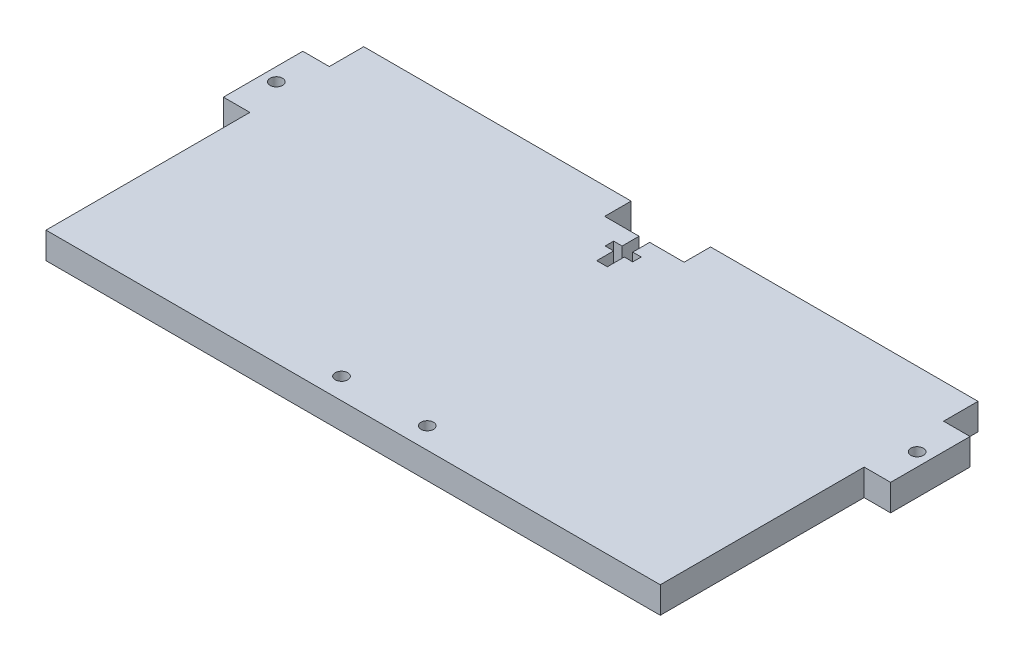
SolidWorks part; units mm, degrees
ref_plane "Front" through (0, 0, 0) normal (0, 0, 1) x (1, 0, 0)
ref_plane "Top" through (0, 0, 0) normal (0, 1, 0) x (1, 0, 0)
ref_plane "Right" through (0, 0, 0) normal (1, 0, 0) x (0, 0, -1)
sketch "Sketch1" plane through (0, 0, 0) normal (0, 1, 0) x (1, 0, 0)
  line L1 (-73.66, -34.925) -> (73.66, -34.925)
  line L2 (-73.66, -34.925) -> (-73.66, 13.97)
  line L3 (-9.525, 34.925) -> (9.525, 34.925)
  line L4 (73.66, -34.925) -> (73.66, 13.97)
  line L5 (-73.66, -34.925) -> (73.66, 34.925) construction
  line L6 (-73.66, 34.925) -> (73.66, -34.925) construction
  line L7 (0, 34.925) -> (0, -34.925) construction
  line L9 (-80.01, 13.97) -> (-73.66, 13.97)
  line L10 (-80.01, 13.97) -> (-80.01, 33.02)
  line L11 (-80.01, 33.02) -> (-73.66, 33.02)
  line L12 (-9.525, 34.925) -> (-9.525, 41.275)
  line L13 (-80.01, 13.97) -> (-73.66, 33.02) construction
  line L14 (-80.01, 33.02) -> (-73.66, 13.97) construction
  line L15 (80.01, 13.97) -> (73.66, 13.97)
  line L16 (80.01, 13.97) -> (80.01, 33.02)
  line L17 (80.01, 33.02) -> (73.66, 33.02)
  line L18 (-73.66, 33.02) -> (-73.66, 34.925)
  line L19 (73.66, 33.02) -> (73.66, 34.925)
  line L20 (-9.525, 41.275) -> (-73.66, 41.275)
  line L21 (-73.66, 34.925) -> (-73.66, 41.275)
  line L22 (9.525, 41.275) -> (73.66, 41.275)
  line L23 (-9.525, 34.925) -> (9.525, 41.275) construction
  line L24 (-9.525, 41.275) -> (9.525, 34.925) construction
  line L25 (9.525, 41.275) -> (9.525, 34.925)
  line L27 (73.66, 41.275) -> (73.66, 34.925)
  circle A0 centre (-76.835, 23.495) radius 1.5
  circle A1 centre (76.835, 23.495) radius 1.5
  point P0 (0, 0)
  point P10 (-76.835, 23.495)
  point P23 (0, 38.1)
  dimension "D5" = 3
  dimension "D8" = 8.255
  dimension "D1" = 147.32
  dimension "D2" = 69.85
  dimension "D3" = 6.35
  dimension "D4" = 19.05
  dimension "D6" = 6.35
  dimension "D7" = 19.05
extrude "Boss-Extrude1" add sketch "Sketch1" along normal blind 6.35
sketch "Sketch2" plane through (0, 6.35, 0) normal (0, 1, 0) x (1, 0, 0)
  line L1 (-11.938, -24.765) -> (-3.81, -24.765) construction
  line L2 (-11.938, -24.765) -> (-11.938, -34.925) construction
  line L3 (-11.938, -34.925) -> (-3.81, -34.925) construction
  line L4 (-3.81, -24.765) -> (-3.81, -34.925) construction
  line L5 (-73.66, -34.925) -> (73.66, -34.925) construction
  line L6 (-73.66, 13.97) -> (-73.66, -34.925) construction
  line L7 (-11.938, -29.845) -> (-7.874, -29.845) construction
  line L8 (-7.874, -29.845) -> (-3.81, -29.845) construction
  circle A0 centre (-7.874, -29.845) radius 1.5
  circle A1 centre (12.7, -29.845) radius 1.5
  dimension "D4" = 3
  dimension "D1" = 61.722
  dimension "D2" = 69.85
  dimension "D3" = 5.08
  dimension "D5" = 20.574
extrude "Cut-Extrude1" cut sketch "Sketch2" against normal through all contours A1 | A0
sketch "Sketch3" plane through (0, 6.35, 0) normal (0, 1, 0) x (1, 0, 0)
  line L0 (0, 34.925) -> (0, 24.765) construction
  line L1 (0, 29.845) -> (-3.302, 29.845) construction
  line L12 (9.525, 34.925) -> (-9.525, 34.925) construction
  line L13 (-1.27, 34.925) -> (1.27, 34.925)
  line L14 (-1.27, 34.925) -> (-1.27, 30.861)
  line L15 (-1.27, 24.765) -> (1.27, 24.765)
  line L16 (1.27, 34.925) -> (1.27, 30.861)
  line L17 (-1.27, 28.829) -> (-1.27, 24.765)
  line L18 (1.27, 30.861) -> (3.302, 30.861)
  line L20 (1.27, 28.829) -> (3.302, 28.829)
  line L21 (3.302, 30.861) -> (3.302, 28.829)
  line L22 (-1.27, 30.861) -> (-3.302, 30.861)
  line L24 (-1.27, 28.829) -> (-3.302, 28.829)
  line L25 (-3.302, 30.861) -> (-3.302, 28.829)
  line L26 (1.27, 28.829) -> (1.27, 24.765)
  point P2 (0, 34.925)
  dimension "D1" = 2.54
  dimension "D2" = 10.16
  dimension "D3" = 6.604
  dimension "D4" = 2.032
extrude "Cut-Extrude2" cut sketch "Sketch3" against normal through all
